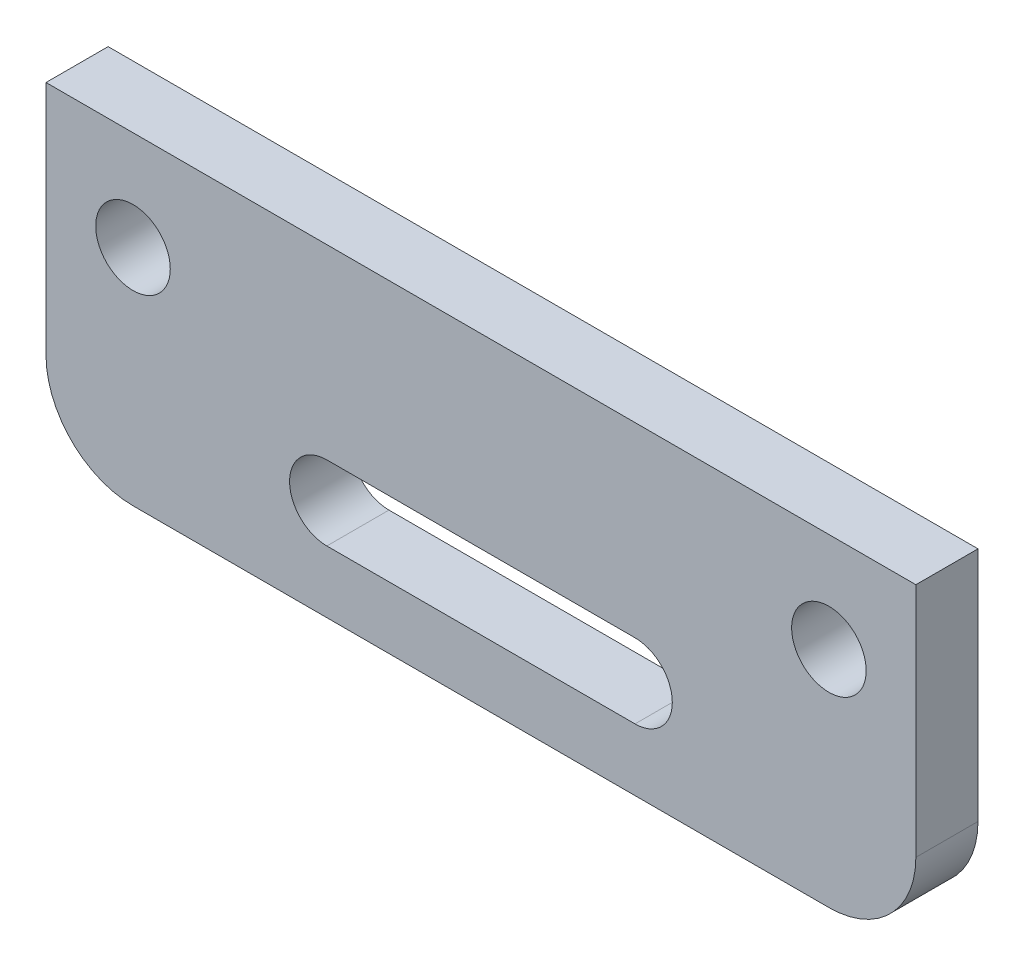
SolidWorks part; units mm, degrees
ref_plane "Front Plane" through (0, 0, 0) normal (0, 0, 1) x (1, 0, 0)
ref_plane "Top Plane" through (0, 0, 0) normal (0, 1, 0) x (1, 0, 0)
ref_plane "Right Plane" through (0, 0, 0) normal (1, 0, 0) x (0, 0, -1)
sketch "Sketch1" plane through (0, 0, 0) normal (0, 0, 1) x (1, 0, 0)
  line L0 (0, -19) -> (0, 26) construction
  line L1 (-11.5, 6) -> (11.5, 6)
  line L2 (-11.5, 6) -> (-11.5, -6)
  line L3 (-11.5, -6) -> (11.5, -6)
  line L4 (11.5, 6) -> (11.5, -6)
  line L5 (-11.5, 6) -> (11.5, -6) construction
  line L6 (-11.5, -6) -> (11.5, 6) construction
  line L7 (-6.2, -15) -> (6.2, -15) construction
  line L8 (-6.2, -13.5) -> (6.2, -13.5)
  line L9 (-6.2, -16.5) -> (6.2, -16.5)
  line L15 (-17.5, 9) -> (17.5, 9) construction
  line L16 (-17.5, 9) -> (-17.5, -19)
  line L17 (-17.5, -19) -> (17.5, -19)
  line L18 (17.5, 9) -> (17.5, -19)
  circle A0 centre (-14, 0) radius 1
  circle A1 centre (-14, -10) radius 1.5
  arc A2 (-6.2, -13.5) -> (-6.2, -16.5) centre (-6.2, -15) ccw
  arc A3 (6.2, -16.5) -> (6.2, -13.5) centre (6.2, -15) ccw
  circle A4 centre (-8.5, 16) radius 2
  circle A5 centre (14, -10) radius 1.5
  circle A6 centre (14, 0) radius 1
  circle A7 centre (8.5, 16) radius 2
  arc A8 (-17.5, 9) -> (17.5, 9) centre (0, 8.4926) cw
  point P0 (0, 0)
  point P13 (0, -15)
  point P19 (-18.5177, -5.388)
  point P27 (0, -19)
  dimension "D6" = 2
  dimension "D8" = 3
  dimension "D10" = 1.5
  dimension "D12" = 4
  dimension "D1" = 23
  dimension "D2" = 12
  dimension "D3" = 45
  dimension "D4" = 13
  dimension "D5" = 2.5
  dimension "D7" = 10
  dimension "D9" = 12.4
  dimension "D11" = 4
  dimension "D13" = 8.5
  dimension "D14" = 10
  dimension "D15" = 28
  dimension "D16" = 35
extrude "Boss-Extrude1" add sketch "Sketch1" along normal blind 2.5
fillet "Fillet1" radius 3.5 2 edges at (-17.5, -19, 1.25) (17.5, -19, 1.25)
sketch "Sketch2" plane through (0, 0, 2.5) normal (0, 0, 1) x (1, 0, 0)
  line L1 (-30.1543, -6) -> (27.7792, -6)
  line L2 (-30.1543, -6) -> (-30.1543, 27.6258)
  line L3 (-30.1543, 27.6258) -> (27.7792, 27.6258)
  line L4 (27.7792, -6) -> (27.7792, 27.6258)
extrude "Cut-Extrude1" cut sketch "Sketch2" against normal blind 10
